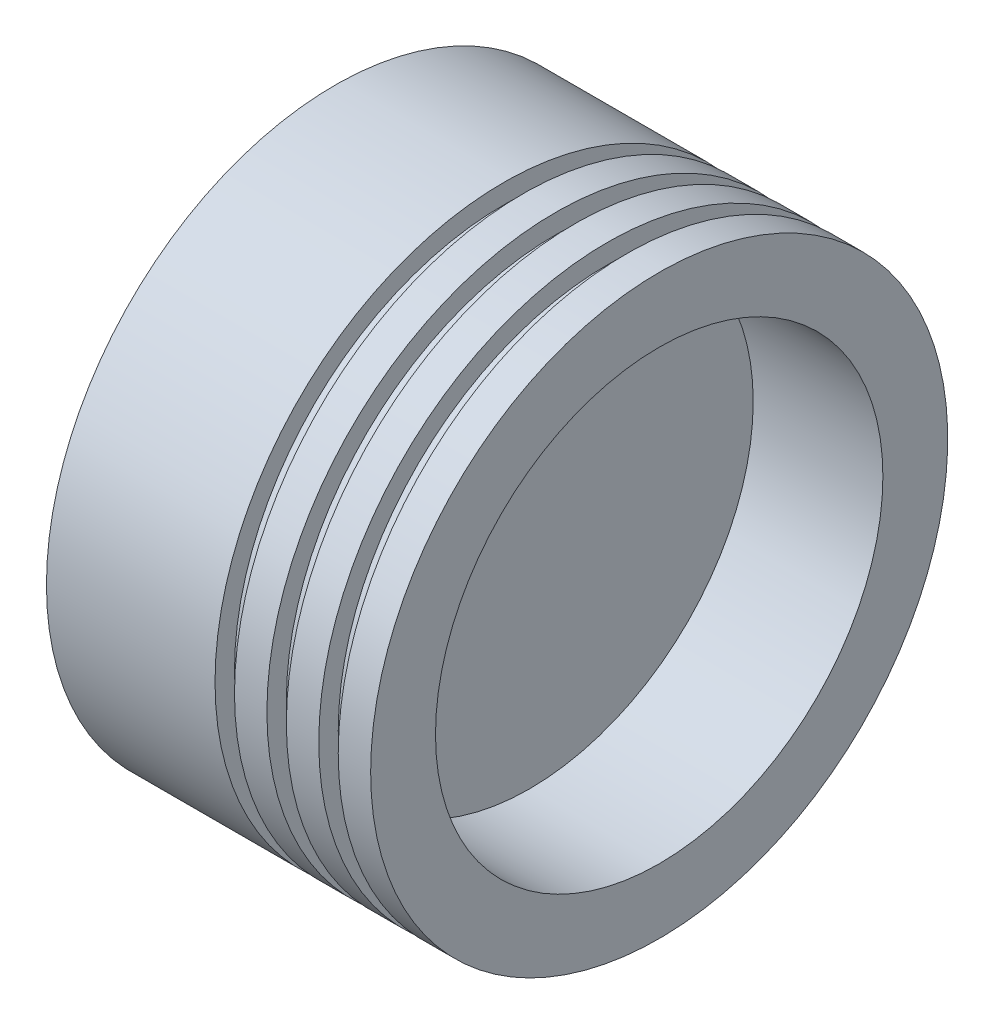
SolidWorks part; units mm, degrees
material "6063-T6"
ref_plane "Front Plane" through (0, 0, 0) normal (0, 0, 1) x (1, 0, 0)
ref_plane "Top Plane" through (0, 0, 0) normal (0, 1, 0) x (1, 0, 0)
ref_plane "Right Plane" through (0, 0, 0) normal (1, 0, 0) x (0, 0, -1)
sketch "Sketch1" plane through (0, 0, 0) normal (0, 0, 1) x (1, 0, 0)
  line L0 (0, 0) -> (30, 0) construction
  line L1 (0, 0) -> (0, 44.5)
  line L2 (0, 44.5) -> (26, 44.5)
  line L3 (26, 44.5) -> (26, 41.5)
  line L4 (26, 41.5) -> (29, 41.5)
  line L5 (29, 41.5) -> (29, 44.5)
  line L6 (29, 44.5) -> (34, 44.5)
  line L7 (34, 44.5) -> (34, 41.5)
  line L8 (34, 41.5) -> (37, 41.5)
  line L9 (37, 41.5) -> (37, 44.5)
  line L10 (37, 44.5) -> (42, 44.5)
  line L11 (42, 44.5) -> (42, 41.5)
  line L12 (42, 41.5) -> (45, 41.5)
  line L13 (45, 41.5) -> (45, 44.5)
  line L14 (45, 44.5) -> (50, 44.5)
  line L15 (50, 44.5) -> (50, 34.5)
  line L16 (50, 34.5) -> (30, 34.5)
  line L17 (30, 34.5) -> (30, 0)
  line L18 (30, 0) -> (0, 0)
  dimension "D1" = 50
  dimension "D2" = 44.5
  dimension "D3" = 26
  dimension "D4" = 3
  dimension "D5" = 5
  dimension "D6" = 3
  dimension "D7" = 10
  dimension "D8" = 20
revolve "Revolve1" add sketch "Sketch1" angle 360 about L0
